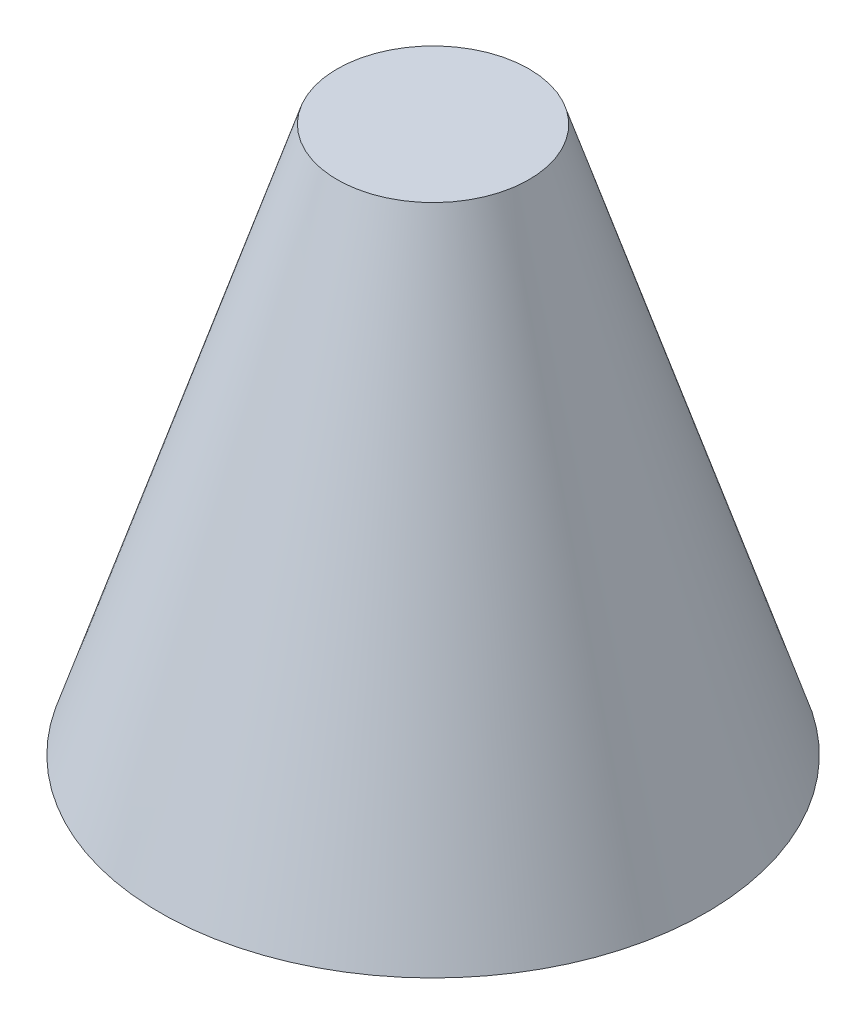
SolidWorks part; units mm, degrees
ref_plane "前视基准面" through (0, 0, 0) normal (0, 0, 1) x (1, 0, 0)
ref_plane "上视基准面" through (0, 0, 0) normal (0, 1, 0) x (1, 0, 0)
ref_plane "右视基准面" through (0, 0, 0) normal (1, 0, 0) x (0, 0, -1)
sketch "草图2" plane through (0, 0, 0) normal (0, 0, 1) x (1, 0, 0)
  line L0 (0, -0.5453) -> (0, 73.4547)
  line L1 (0, 73.4547) -> (13, 73.4547)
  line L2 (13, 73.4547) -> (37, -0.5453)
  line L3 (37, -0.5453) -> (0, -0.5453)
  dimension "D1" = 37
  dimension "D2" = 74
  dimension "D3" = 13
revolve "旋转1" add sketch "草图2" angle 360 about L0
